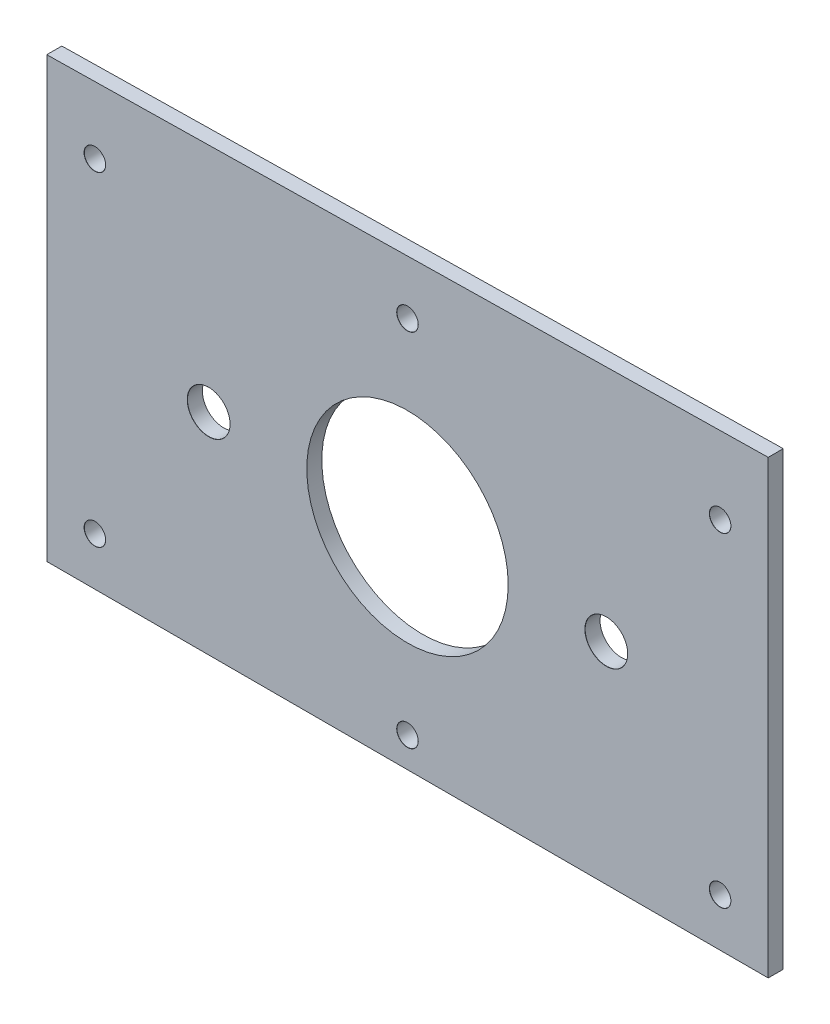
SolidWorks part; units mm, degrees
material "Alloy Steel (SS)"
ref_plane "X-Y Datum" through (0, 0, 0) normal (0, 0, 1) x (1, 0, 0)
ref_plane "X-Z Datum" through (0, 0, 0) normal (0, 1, 0) x (1, 0, 0)
ref_plane "Y-Z Datum" through (0, 0, 0) normal (1, 0, 0) x (0, 0, -1)
sketch "Sketch1" plane through (0, 0, 0) normal (0, 0, 1) x (1, 0, 0)
  line L0 (-76.2, 48.26) -> (-76.2, 44.45)
  line L1 (-76.2, 44.45) -> (76.2, 44.45) construction
  line L2 (-76.2, 44.45) -> (-76.2, -44.45)
  line L3 (-76.2, -44.45) -> (76.2, -44.45)
  line L4 (76.2, 44.45) -> (76.2, -44.45)
  line L5 (-76.2, 44.45) -> (76.2, -44.45) construction
  line L6 (-76.2, -44.45) -> (76.2, 44.45) construction
  line L7 (76.2, 44.45) -> (76.2, 50.8)
  line L10 (-76.2, 48.26) -> (76.2, 50.8)
  point P0 (0, 0)
  dimension "D1" = 152.4
  dimension "D2" = 88.9
  dimension "D3" = 6.35
  dimension "D4" = 3.81
extrude "Boss-Extrude1" add sketch "Sketch1" along normal blind 3.175
hole_wizard "M4 Clearance Hole1" positions "Sketch7" profile "Sketch8" hole size "M4" standard "ANSI Metric" end condition through all
sketch "Sketch7" plane through (0, 0, 3.175) normal (0, 0, 1) x (1, 0, 0)
  line L0 (-75.8701, 0) -> (49924.1299, 0) construction
  line L1 (0, 56.7764) -> (0, -49943.2236) construction
  line L2 (-76.2, -44.45) -> (76.2, -44.45) construction
  line L10 (-76.2, 0) -> (76.2, 0) construction
  line L11 (-76.2, 48.26) -> (-76.2, -44.45) construction
  line L12 (76.2, -44.45) -> (76.2, 50.8) construction
  line L14 (-69.85, -44.45) -> (-69.85, 48.3658) construction
  line L15 (-76.2, -44.45) -> (76.2, -44.45) construction
  line L16 (76.2, 50.8) -> (-76.2, 48.26) construction
  line L17 (69.85, -44.45) -> (69.85, 50.6942) construction
  line L18 (66.04, -44.45) -> (66.04, 50.6307) construction
  line L20 (-66.04, -44.45) -> (-66.04, 48.4293) construction
  line L21 (-76.2, -38.1) -> (76.2, -38.1) construction
  line L22 (-76.2, 34.29) -> (76.2, 34.29) construction
  line L23 (-76.2, -34.29) -> (76.2, -34.29) construction
  line L24 (-76.2, 38.1) -> (76.2, 38.1) construction
  circle A10 centre (-66.04, 34.29) radius 6.35
  circle A11 centre (-66.04, -34.29) radius 6.35
  circle A12 centre (0, -38.1) radius 6.35
  circle A13 centre (66.04, -34.29) radius 6.35
  circle A14 centre (66.04, 34.29) radius 6.35
  circle A15 centre (0, 38.1) radius 6.35
  circle A16 centre (-69.85, 0) radius 6.35
  circle A17 centre (69.85, 0) radius 6.35
  point P174 (-66.04, 34.29)
  point P176 (-66.04, -34.29)
  point P178 (0, -38.1)
  point P180 (66.04, -34.29)
  point P182 (66.04, 34.29)
  point P184 (0, 38.1)
  dimension "D1" = 6.35
  dimension "D9" = 12.7
  dimension "D2" = 146.05
  dimension "D3" = 142.24
  dimension "D4" = 6.35
  dimension "D5" = 10.16
  dimension "D6" = 10.16
  dimension "D7" = 78.74
  dimension "D8" = 82.55
sketch "Sketch8" plane through (0, 38.1, 3.175) normal (1, 0, 0) x (0, -1, 0)
  line L0 (0, 0) -> (0, 3.175)
  line L1 (0, 3.175) -> (2.25, 3.175)
  line L2 (2.25, 3.175) -> (2.25, 0.025)
  line L3 (2.25, 0.025) -> (2.275, 0)
  line L5 (2.275, 0) -> (0, 0)
  line L6 (-2.25, 0.025) -> (-2.275, 0) construction
  line L11 (0, -6.35) -> (0, 107.95) construction
  dimension "Thru Hole Dia." = 4.5
  dimension "Thru Hole Depth" = 3.175
  dimension "Near C'Sink Dia." = 4.55
  dimension "Near C'Sink Angle" = 90
sketch "Sketch9" plane through (0, 0, 3.175) normal (0, 0, 1) x (1, 0, 0)
  line L0 (-42, 0) -> (42, 0) construction
  line L1 (0, -44.45) -> (0, 42.6782) construction
  line L2 (-76.2, -44.45) -> (76.2, -44.45) construction
  circle A0 centre (0, 0) radius 21.275
  circle A1 centre (42, 0) radius 4 construction
  circle A2 centre (-42, 0) radius 4 construction
  dimension "D1" = 42.55
  dimension "D3" = 8
  dimension "D2" = 42
hole_wizard "M8 Clearance Hole1" positions "Sketch10" profile "Sketch11" hole size "M8" standard "ANSI Metric" end condition through all
sketch "Sketch10" plane through (0, 0, 3.175) normal (0, 0, 1) x (1, 0, 0)
  point P0 (-42, 0)
  point P3 (42, 0)
sketch "Sketch11" plane through (-42, 0, 3.175) normal (1, 0, 0) x (0, -1, 0)
  line L0 (0, 0) -> (0, 3.175)
  line L1 (0, 3.175) -> (4.5, 3.175)
  line L2 (4.5, 3.175) -> (4.5, 0.025)
  line L3 (4.5, 0.025) -> (4.525, 0)
  line L5 (4.525, 0) -> (0, 0)
  line L6 (-4.5, 0.025) -> (-4.525, 0) construction
  line L11 (0, -6.35) -> (0, 107.95) construction
  dimension "Thru Hole Dia." = 9
  dimension "Thru Hole Depth" = 3.175
  dimension "Near C'Sink Dia." = 9.05
  dimension "Near C'Sink Angle" = 90
extrude "Center Hole" cut sketch "Sketch9" against normal through all
